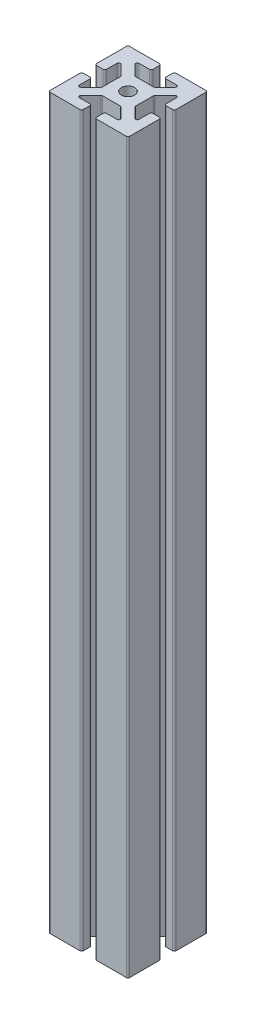
SolidWorks part; units mm, degrees
ref_plane "Front Plane" through (0, 0, 0) normal (0, 0, 1) x (1, 0, 0)
ref_plane "Top Plane" through (0, 0, 0) normal (0, 1, 0) x (1, 0, 0)
ref_plane "Right Plane" through (0, 0, 0) normal (1, 0, 0) x (0, 0, -1)
sketch "Sketch1" plane through (0, 0, 0) normal (0, 1, 0) x (1, 0, 0)
  line L1 (-6, -6) -> (-1, -6)
  line L2 (-6, -6) -> (-6, -1)
  line L3 (-6, 6) -> (-1, 6)
  line L4 (6, -6) -> (6, -1)
  line L7 (-1.4393, -2.5) -> (1.4393, -2.5)
  line L8 (-2.5, -1.4393) -> (-2.5, 1.4393)
  line L9 (-1.4393, 2.5) -> (1.4393, 2.5)
  line L10 (2.5, -1.4393) -> (2.5, 1.4393)
  line L11 (0, 0) -> (-2.5, 0) construction
  line L12 (-4.5, 1) -> (-6, 1)
  line L16 (-3.4393, 4.5) -> (-1, 4.5)
  line L17 (4.5, -3.4393) -> (4.5, -1)
  line L18 (-3.4393, -4.5) -> (-1, -4.5)
  line L19 (-4.5, -3.4393) -> (-4.5, -1)
  line L20 (-4.5, 3.4393) -> (-2.5, 1.4393)
  line L21 (-3.4393, -4.5) -> (-1.4393, -2.5)
  line L22 (-3.4393, 4.5) -> (-1.4393, 2.5)
  line L23 (-4.5, -3.4393) -> (-2.5, -1.4393)
  line L30 (1.4393, 2.5) -> (3.4393, 4.5)
  line L31 (1.4393, -2.5) -> (3.4393, -4.5)
  line L34 (2.5, -1.4393) -> (4.5, -3.4393)
  line L35 (2.5, 1.4393) -> (4.5, 3.4393)
  line L36 (-5.0573, 0) -> (-4.5, 0) construction
  line L37 (0, 0) -> (0, 1.255) construction
  line L38 (-4.5, -1) -> (-6, -1)
  line L40 (1, 4.5) -> (1, 6)
  line L41 (-1, 4.5) -> (-1, 6)
  line L42 (4.5, -1) -> (6, -1)
  line L43 (4.5, 1) -> (6, 1)
  line L44 (-1, -4.5) -> (-1, -6)
  line L45 (1, -4.5) -> (1, -6)
  line L46 (-6, 1) -> (-6, 6)
  line L47 (-6, -6) -> (-6, 6) construction
  line L48 (-4.5, 1) -> (-4.5, 3.4393)
  line L49 (-4.5, -4.5) -> (-4.5, 4.5) construction
  line L50 (-4.5, 0) -> (-5.0573, 0) construction
  line L51 (-2.5, 0) -> (0, 0) construction
  line L52 (1, -4.5) -> (3.4393, -4.5)
  line L53 (-4.5, -4.5) -> (4.5, -4.5) construction
  line L54 (1, -6) -> (6, -6)
  line L55 (-6, -6) -> (6, -6) construction
  line L56 (4.5, 1) -> (4.5, 3.4393)
  line L57 (4.5, -4.5) -> (4.5, 4.5) construction
  line L58 (6, 1) -> (6, 6)
  line L59 (6, -6) -> (6, 6) construction
  line L60 (1, 4.5) -> (3.4393, 4.5)
  line L61 (-4.5, 4.5) -> (4.5, 4.5) construction
  line L62 (1, 6) -> (6, 6)
  line L63 (-6, 6) -> (6, 6) construction
  circle A0 centre (0, 0) radius 1
  circle A1 centre (0, 0) radius 1
  circle A2 centre (0, 0) radius 1
  circle A3 centre (0, 0) radius 1
  point P0 (0, 0)
  point P7 (0, 0)
  point P65 (0, 0)
  dimension "D7" = 2
  dimension "D1" = 2.5
  dimension "D2" = 3.5
  dimension "D6" = 1
  dimension "D4" = 1.5
  dimension "D8" = 4
extrude "Boss-Extrude2" add sketch "Sketch1" along normal mid plane 110 contours L62 L40 L60 L30 L9 L22 L16 L41 L3 L46 L12 L48 L20 L8 L23 L19 L38 L2 L1 L44 L18 L21 L7 L31 L52 L45 L54 L4 L42 L17 L34 L10 L35 L56 L43 L58 A0
fillet "Fillet2" radius 0.25 36 edges at (4.5, 0, -1) (4.5, 0, -3.4393) (2.5, 0, -1.4393) (2.5, 0, 1.4393) (4.5, 0, 3.4393) (4.5, 0, 1) (6, 0, 1) (6, 0, 6) (1, 0, 6) (1, 0, 4.5) (3.4393, 0, 4.5) (1.4393, 0, 2.5) (-1.4393, 0, 2.5) (-3.4393, 0, 4.5) (-1, 0, 4.5) (-1, 0, 6) (-6, 0, 6) (-6, 0, 1) (-4.5, 0, 1) (-4.5, 0, 3.4393) (-2.5, 0, 1.4393) (-2.5, 0, -1.4393) (-4.5, 0, -3.4393) (-4.5, 0, -1) (-6, 0, -1) (-6, 0, -6) (-1, 0, -6) (-1, 0, -4.5) (-3.4393, 0, -4.5) (-1.4393, 0, -2.5) (1.4393, 0, -2.5) (3.4393, 0, -4.5) (1, 0, -4.5) (6, 0, -6) (1, 0, -6) (6, 0, -1)
